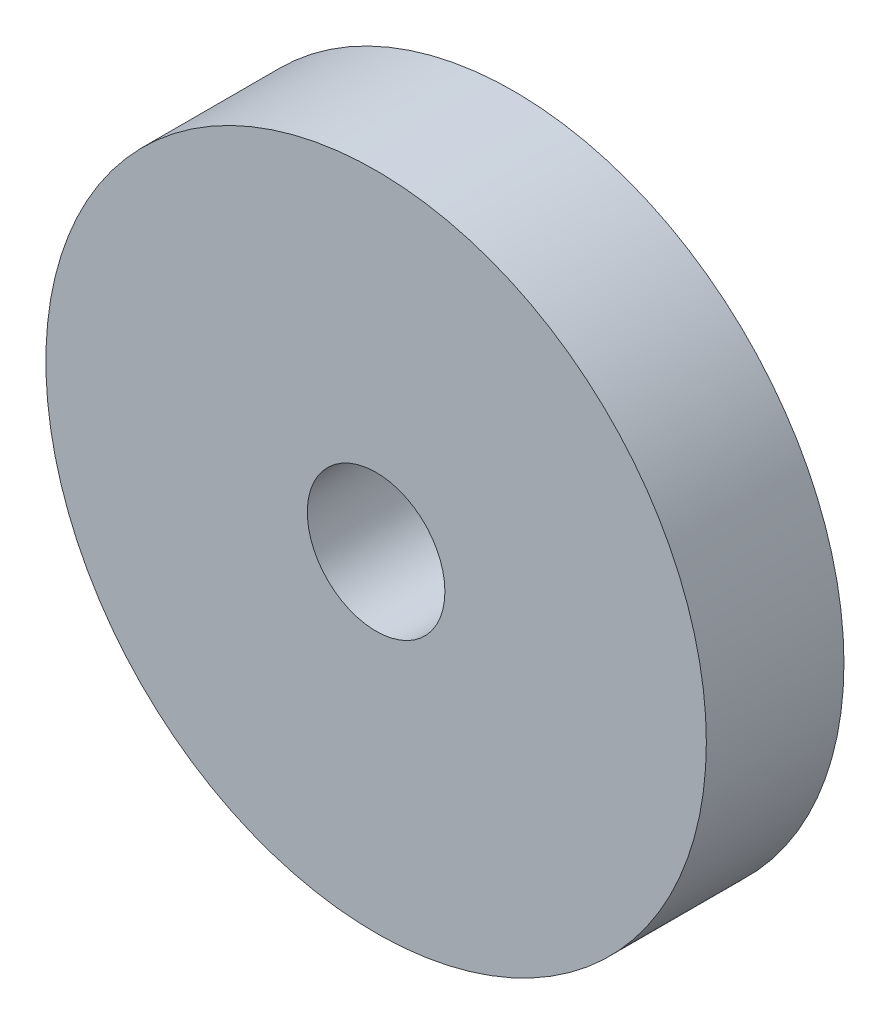
SolidWorks part; units mm, degrees
ref_plane "Front" through (0, 0, 0) normal (0, 0, 1) x (1, 0, 0)
ref_plane "Top" through (0, 0, 0) normal (0, 1, 0) x (1, 0, 0)
ref_plane "Right" through (0, 0, 0) normal (1, 0, 0) x (0, 0, -1)
sketch "Sketch1" plane through (0, 0, 0) normal (0, 0, 1) x (1, 0, 0)
  circle A0 centre (0, 0) radius 38.1
  circle A1 centre (0, 0) radius 7.9375
  dimension "D1" = 76.2
  dimension "D2" = 15.875
extrude "Boss-Extrude1" add sketch "Sketch1" along normal blind 15.875
